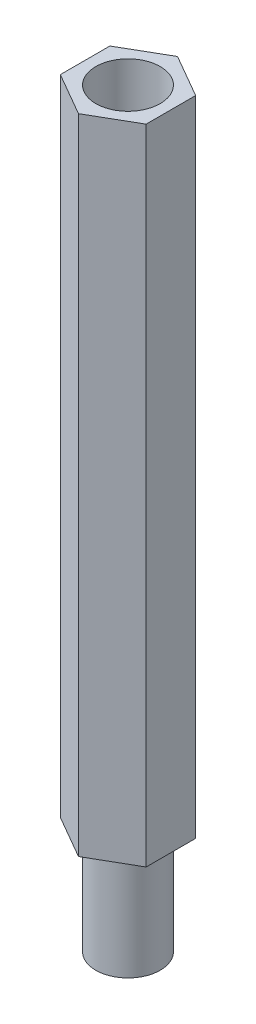
SolidWorks part; units mm, degrees
ref_plane "前视基准面" through (0, 0, 0) normal (0, 0, 1) x (1, 0, 0)
ref_plane "上视基准面" through (0, 0, 0) normal (0, 1, 0) x (1, 0, 0)
ref_plane "右视基准面" through (0, 0, 0) normal (1, 0, 0) x (0, 0, -1)
sketch "草图1" plane through (0, 0, 0) normal (0, 1, 0) x (1, 0, 0)
  circle A0 centre (0, 0) radius 1.5
extrude "凸台-拉伸1" add sketch "草图1" along normal blind 5
sketch "草图2" plane through (0, 5, 0) normal (0, 1, 0) x (1, 0, 0)
  line L1 (0, 2.3094) -> (-2, 1.1547)
  line L2 (-2, 1.1547) -> (-2, -1.1547)
  line L3 (-2, -1.1547) -> (0, -2.3094)
  line L4 (0, -2.3094) -> (2, -1.1547)
  line L5 (2, -1.1547) -> (2, 1.1547)
  line L6 (2, 1.1547) -> (0, 2.3094)
  circle A0 centre (0, 0) radius 2 construction
extrude "凸台-拉伸2" add sketch "草图2" along normal blind 30
sketch "草图3" plane through (0, 35, 0) normal (0, 1, 0) x (1, 0, 0)
  circle A0 centre (0, 0) radius 1.5
extrude "切除-拉伸1" cut sketch "草图3" against normal blind 5
